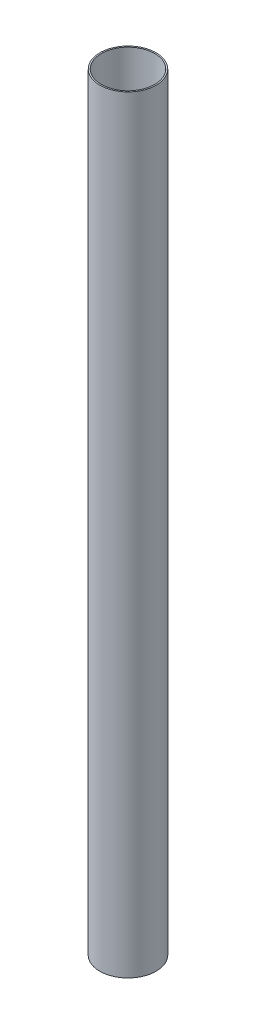
SolidWorks part; units mm, degrees
ref_plane "Спереди" through (0, 0, 0) normal (0, 0, 1) x (1, 0, 0)
ref_plane "Сверху" through (0, 0, 0) normal (0, 1, 0) x (1, 0, 0)
ref_plane "Справа" through (0, 0, 0) normal (1, 0, 0) x (0, 0, -1)
sketch "Эскиз2" plane through (0, 0, 0) normal (0, 1, 0) x (1, 0, 0)
  circle A0 centre (0, 0) radius 55
extrude "Вытянуть-Тонкостенный1" add sketch "Эскиз2" along normal blind 1500 thin thin type one direction reverse wall 2.7
